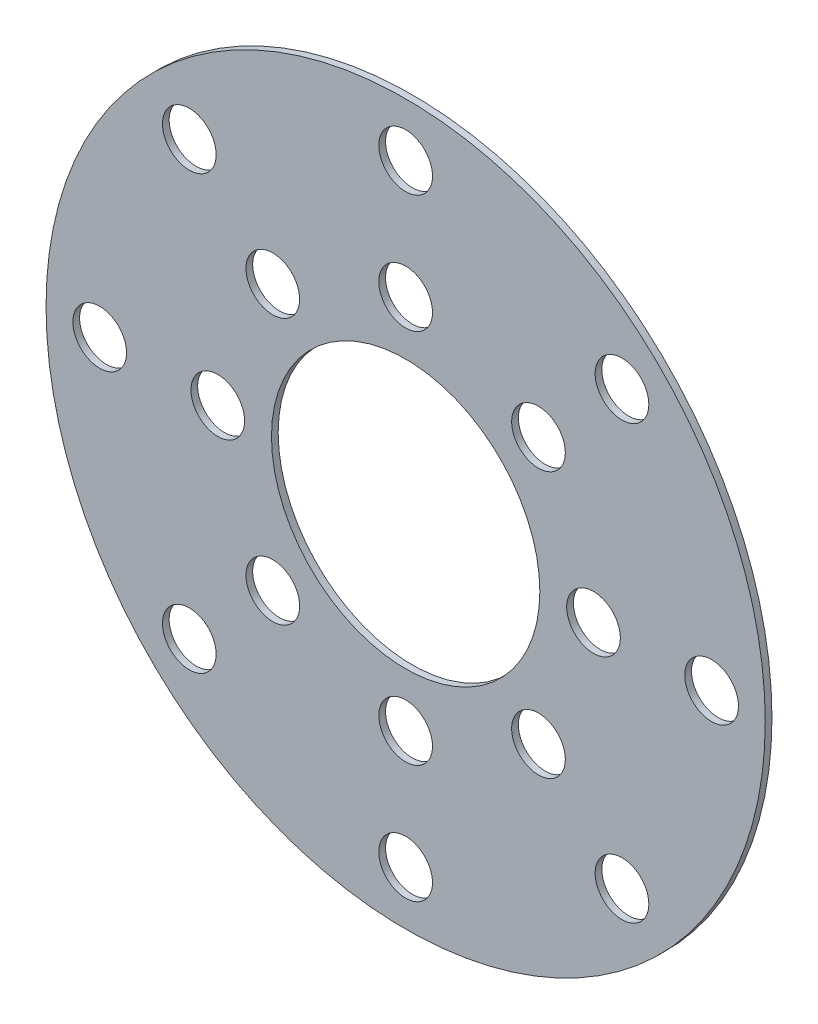
SolidWorks part; units mm, degrees
material "Epoxy, Unfilled"
ref_plane "Front Plane" through (0, 0, 0) normal (0, 0, 1) x (1, 0, 0)
ref_plane "Top Plane" through (0, 0, 0) normal (0, 1, 0) x (1, 0, 0)
ref_plane "Right Plane" through (0, 0, 0) normal (1, 0, 0) x (0, 0, -1)
sketch "Sketch4" plane through (0, 0, 0) normal (0, 0, 1) x (1, 0, 0)
  circle A0 centre (0, 0) radius 42.545
  dimension "D1" = 85.09
extrude "Boss-Extrude2" add sketch "Sketch4" along normal blind 0.7937
sketch "Sketch5" plane through (0, 0, 0.7937) normal (0, 0, 1) x (1, 0, 0)
  circle A0 centre (0, 0) radius 15.875
  dimension "D1" = 31.75
extrude "Cut-Extrude5" cut sketch "Sketch5" against normal through all
sketch "Sketch9" plane through (0, 0, 0.7937) normal (0, 0, 1) x (1, 0, 0)
  line L0 (0, 0) -> (36.195, 0) construction
  line L1 (0, 0) -> (25.5937, 25.5937) construction
  line L2 (0, 0) -> (25.5937, -25.5937) construction
  circle A0 centre (22.225, 0) radius 3.175
  circle A1 centre (36.195, 0) radius 3.175
  circle A4 centre (0, 0) radius 15.875 construction
  circle A6 centre (15.7154, -15.7154) radius 3.175
  circle A7 centre (25.5937, -25.5937) radius 3.175
  circle A10 centre (0, -22.225) radius 3.175
  circle A11 centre (0, -36.195) radius 3.175
  circle A14 centre (-15.7154, -15.7154) radius 3.175
  circle A15 centre (-25.5937, -25.5937) radius 3.175
  circle A18 centre (-22.225, 0) radius 3.175
  circle A19 centre (-36.195, 0) radius 3.175
  circle A22 centre (-15.7154, 15.7154) radius 3.175
  circle A23 centre (-25.5937, 25.5937) radius 3.175
  circle A26 centre (0, 22.225) radius 3.175
  circle A27 centre (0, 36.195) radius 3.175
  circle A30 centre (15.7154, 15.7154) radius 3.175
  circle A31 centre (25.5937, 25.5937) radius 3.175
  point P74 (0, 0)
  point P87 (0, 0)
  dimension "D1" = 13.97
  dimension "D2" = 6.35
  dimension "D4" = 6.35
  dimension "D8" = 45
  dimension "D9" = 45
  dimension "D7" = 8
extrude "Cut-Extrude12" cut sketch "Sketch9" against normal through all
equation "\"CoilSep\"= 1.005"
